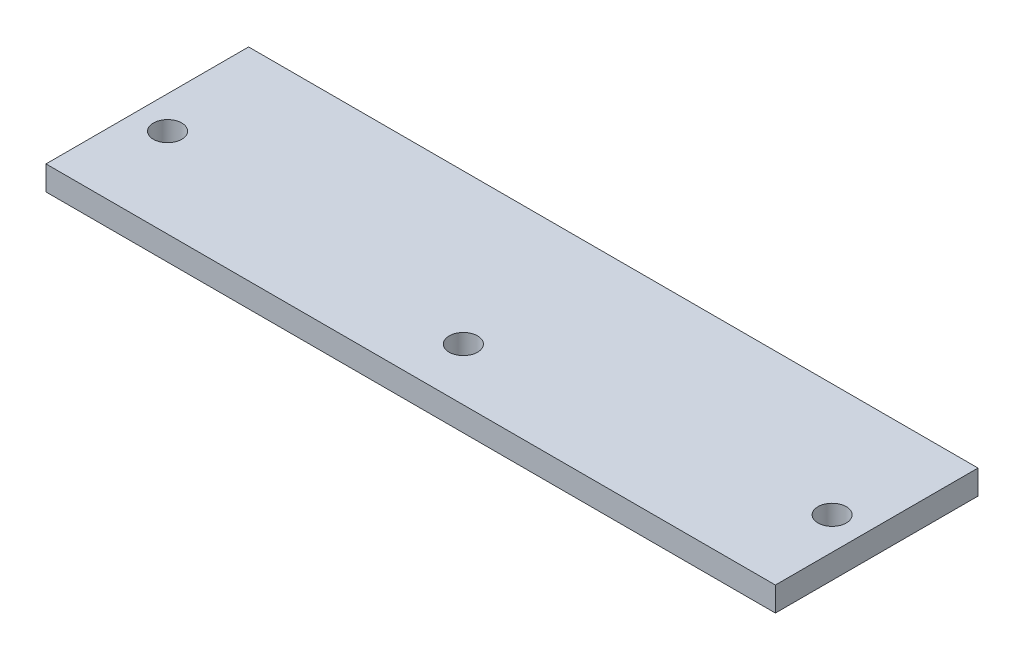
SolidWorks part; units mm, degrees
ref_plane "Plan de face" through (0, 0, 0) normal (0, 0, 1) x (1, 0, 0)
ref_plane "Plan de dessus" through (0, 0, 0) normal (0, 1, 0) x (1, 0, 0)
ref_plane "Plan de droite" through (0, 0, 0) normal (1, 0, 0) x (0, 0, -1)
sketch "Esquisse1" plane through (0, 0, 0) normal (0, 1, 0) x (1, 0, 0)
  line L0 (0, 0) -> (0, -1.5) construction
  line L1 (-45, 12.5) -> (45, 12.5)
  line L2 (-45, 12.5) -> (-45, -12.5)
  line L3 (-45, -12.5) -> (45, -12.5)
  line L4 (45, 12.5) -> (45, -12.5)
  line L5 (-45, 12.5) -> (45, -12.5) construction
  line L6 (-45, -12.5) -> (45, 12.5) construction
  line L7 (41, -1.5) -> (-41, -1.5) construction
  line L8 (0, 0) -> (0, -6) construction
  circle A0 centre (-41, -1.5) radius 1.75
  circle A1 centre (41, -1.5) radius 1.75
  circle A2 centre (0, -6) radius 1.75
  point P0 (0, 0)
  point P11 (0, -1.5)
  point P15 (0, -6)
  dimension "D3" = 1.5
  dimension "D5" = 3.5
  dimension "D1" = 90
  dimension "D2" = 25
  dimension "D4" = 82
  dimension "D6" = 6
extrude "Boss.-Extru.1" add sketch "Esquisse1" along normal blind 3
